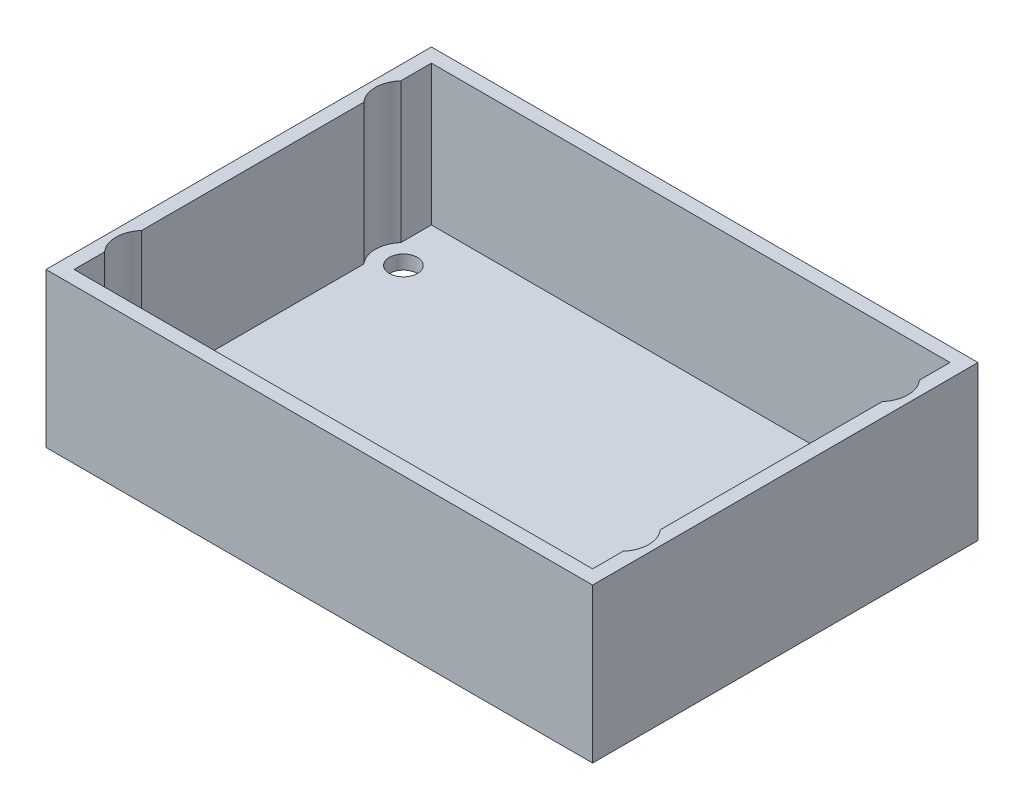
SolidWorks part; units mm, degrees
ref_plane "前视基准面" through (0, 0, 0) normal (0, 0, 1) x (1, 0, 0)
ref_plane "上视基准面" through (0, 0, 0) normal (0, 1, 0) x (1, 0, 0)
ref_plane "右视基准面" through (0, 0, 0) normal (1, 0, 0) x (0, 0, -1)
sketch "草图1" plane through (0, 0, 0) normal (0, 1, 0) x (1, 0, 0)
  line L1 (0, 0) -> (78, 0)
  line L2 (0, 0) -> (0, 55)
  line L3 (0, 55) -> (78, 55)
  line L4 (78, 0) -> (78, 55)
extrude "凸台-拉伸1" add sketch "草图1" along normal blind 22
sketch "草图2" plane through (0, 22, 0) normal (0, 1, 0) x (1, 0, 0)
  line L1 (2, 2) -> (76, 2)
  line L2 (2, 2) -> (2, 53)
  line L3 (2, 53) -> (76, 53)
  line L4 (76, 2) -> (76, 53)
extrude "切除-拉伸1" cut sketch "草图2" against normal blind 20
sketch "草图4" plane through (0, 22, 0) normal (0, 1, 0) x (1, 0, 0)
  circle A0 centre (5, 9) radius 4
  circle A1 centre (5, 46) radius 4
  circle A2 centre (73, 46) radius 4
  circle A3 centre (73, 9) radius 4
extrude "切除-拉伸2" cut sketch "草图4" against normal blind 20
sketch "草图5" plane through (0, 22, 0) normal (0, 1, 0) x (1, 0, 0)
  circle A0 centre (5, 9) radius 2
  circle A1 centre (5, 46) radius 2
  circle A2 centre (73, 46) radius 2
  circle A3 centre (73, 9) radius 2
extrude "切除-拉伸4" cut sketch "草图5" against normal through all
